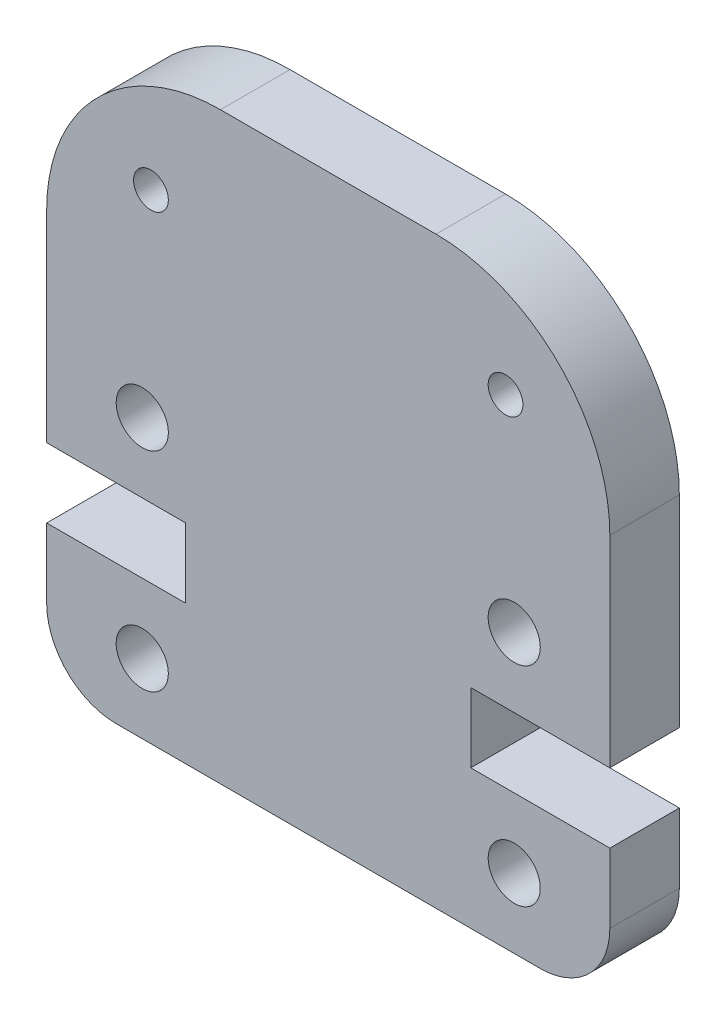
SolidWorks part; units mm, degrees
ref_plane "Front Plane" through (0, 0, 0) normal (0, 0, 1) x (1, 0, 0)
ref_plane "Top Plane" through (0, 0, 0) normal (0, 1, 0) x (1, 0, 0)
ref_plane "Right Plane" through (0, 0, 0) normal (1, 0, 0) x (0, 0, -1)
sketch "Sketch1" plane through (0, 0, 0) normal (0, 0, 1) x (1, 0, 0)
  line L0 (0, 6) -> (0, 11.795)
  line L1 (12.2, 4) -> (16.2, 4)
  line L2 (5, 16.795) -> (11.2, 16.795)
  line L3 (2, 0) -> (14.2, 0)
  line L4 (12.2, 6) -> (12.2, 4)
  line L5 (0, 2) -> (0, 4)
  line L6 (0, 6) -> (4, 6)
  line L7 (16.2, 6) -> (12.2, 6)
  line L8 (4, 6) -> (4, 4)
  line L9 (4, 4) -> (0, 4)
  line L10 (16.2, 2) -> (16.2, 4)
  line L11 (16.2, 6) -> (16.2, 11.795)
  line L12 (8.1, 16.795) -> (8.1, 0) construction
  circle A0 centre (13.45, 2) radius 0.75
  arc A1 (5, 16.795) -> (0, 11.795) centre (5, 11.795) ccw
  circle A2 centre (13.45, 8) radius 0.75
  circle A3 centre (3, 13.795) radius 0.5
  arc A4 (16.2, 2) -> (14.2, 0) centre (14.2, 2) cw
  arc A5 (0, 2) -> (2, 0) centre (2, 2) ccw
  circle A6 centre (13.2, 13.795) radius 0.5
  circle A7 centre (2.75, 8) radius 0.75
  arc A8 (11.2, 16.795) -> (16.2, 11.795) centre (11.2, 11.795) cw
  circle A9 centre (2.75, 2) radius 0.75
  dimension "D1" = 1.5
  dimension "D2" = 1
  dimension "D3" = 5
  dimension "D4" = 2
  dimension "D5" = 3
  dimension "D6" = 8.1
  dimension "D7" = 8
  dimension "D8" = 3
  dimension "D9" = 16.795
extrude "Boss-Extrude1" add sketch "Sketch1" along normal blind 2
equation "\"D6@Sketch1\"= \"fingerWidth@parametersSketch@prostheticParameters.SLDPRT\" / 2 'DIP width"
equation "\"D9@Sketch1\"= \"HL@parametersSketch@prostheticParameters.SLDPRT\" * 0.107 - 3 'DIP length - Sil. Sht DIP"
